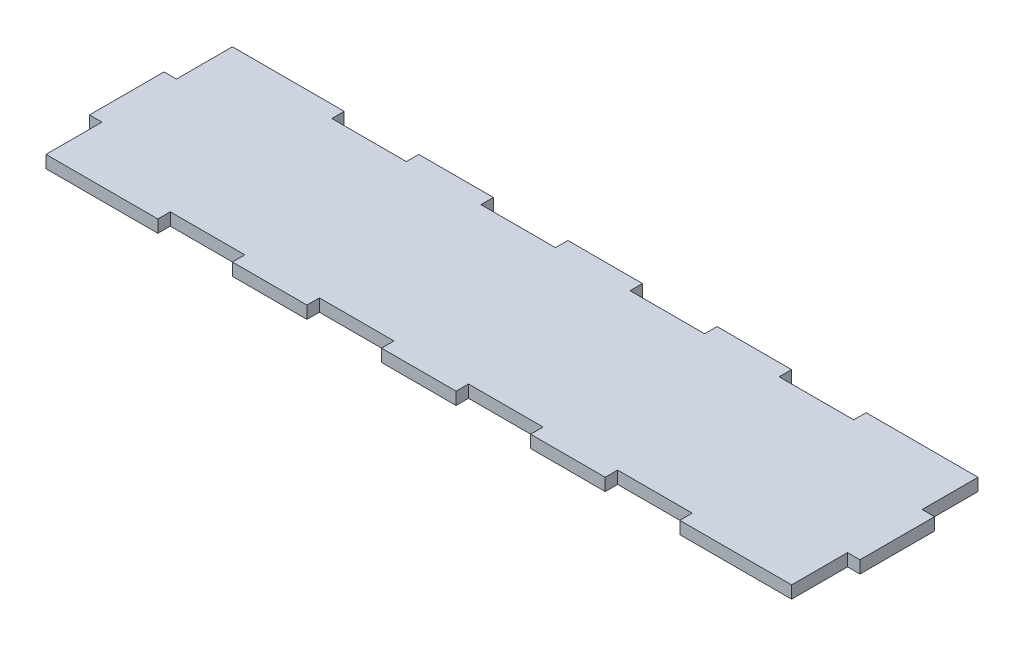
SolidWorks part; units mm, degrees
ref_plane "Plan de face" through (0, 0, 0) normal (0, 0, 1) x (1, 0, 0)
ref_plane "Plan de dessus" through (0, 0, 0) normal (0, 1, 0) x (1, 0, 0)
ref_plane "Plan de droite" through (0, 0, 0) normal (1, 0, 0) x (0, 0, -1)
sketch "Esquisse2" plane through (0, 0, 0) normal (0, 1, 0) x (1, 0, 0)
  line L1 (-190.5, 47.625) -> (190.5, 47.625)
  line L2 (-190.5, 47.625) -> (-190.5, -47.625)
  line L3 (-190.5, -47.625) -> (190.5, -47.625)
  line L4 (190.5, 47.625) -> (190.5, -47.625)
  point P4 (235.8571, -90.7143)
  point P5 (0, 47.625)
  point P7 (190.5, 0)
  dimension "D1" = 381
  dimension "D2" = 95.25
extrude "Boss.-Extru.1" add sketch "Esquisse2" along normal blind 6.35
sketch "Esquisse3" plane through (190.5, 0, 0) normal (1, 0, 0) x (0, 0, -1)
  line L0 (-47.625, 6.35) -> (47.625, 6.35) construction
  line L1 (-19.05, 6.35) -> (19.05, 6.35)
  line L2 (-19.05, 6.35) -> (-19.05, 0)
  line L3 (-19.05, 0) -> (19.05, 0)
  line L4 (19.05, 6.35) -> (19.05, 0)
  line L5 (-47.625, 0) -> (47.625, 0) construction
  line L6 (47.625, 6.35) -> (47.625, 0) construction
  dimension "D1" = 38.1
  dimension "D2" = 28.575
extrude "Boss.-Extru.2" add sketch "Esquisse3" along normal blind 6.35
sketch "Esquisse4" plane through (0, 0, -47.625) normal (0, 0, -1) x (-1, 0, 0)
  line L0 (-190.5, 6.35) -> (190.5, 6.35) construction
  line L1 (-133.35, 6.35) -> (-95.25, 6.35)
  line L2 (-133.35, 6.35) -> (-133.35, 0)
  line L3 (-133.35, 0) -> (-95.25, 0)
  line L4 (-95.25, 6.35) -> (-95.25, 0)
  line L5 (-190.5, 0) -> (190.5, 0) construction
  line L6 (-190.5, 6.35) -> (-190.5, 0) construction
  dimension "D1" = 38.1
  dimension "D2" = 57.15
extrude "Enlèv. mat.-Extru.1" cut sketch "Esquisse4" against normal blind 6.35
pattern_linear "Répétition linéaire1" count 4 spacing 76.2 along (-1, 0, 0) count 2 spacing 88.9 along (0, 0, 1) of "Enlèv. mat.-Extru.1"
mirror "Symétrie1" about plane through (0, 0, 0) normal (1, 0, 0) of "Boss.-Extru.2"
